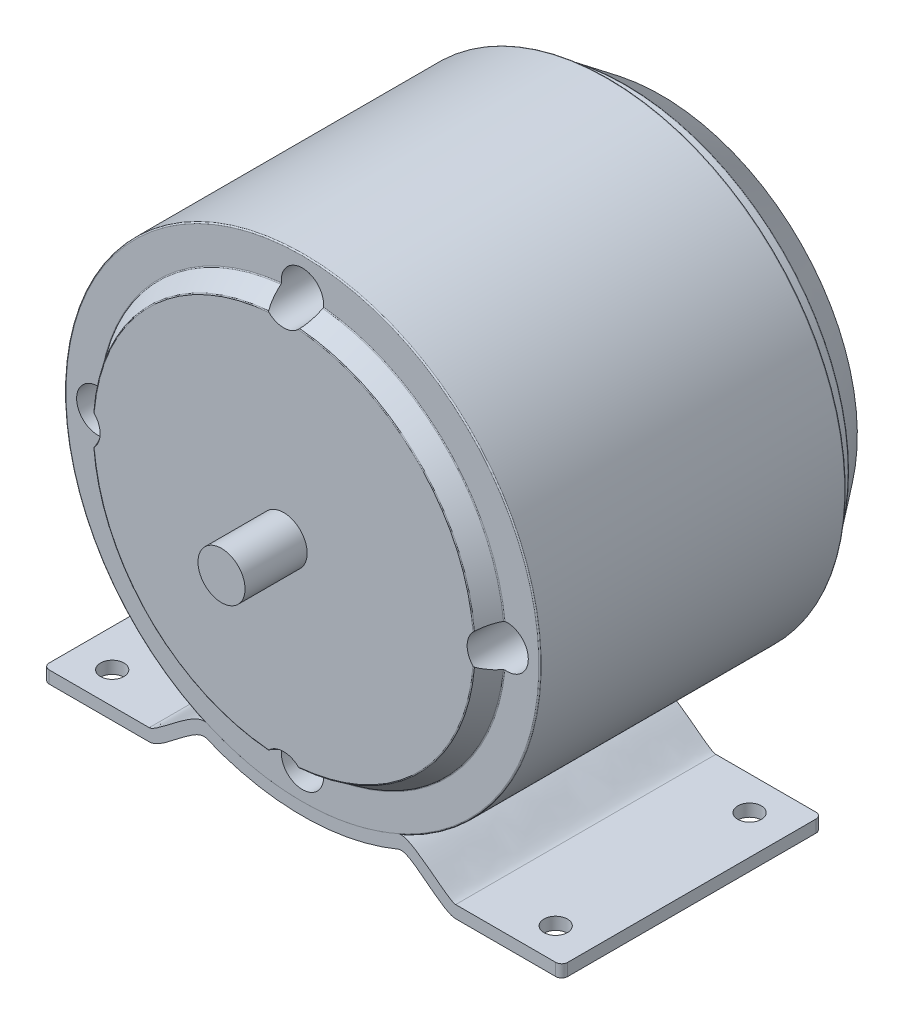
SolidWorks part; units mm, degrees
ref_plane "Front Plane" through (0, 0, 0) normal (0, 0, 1) x (1, 0, 0)
ref_plane "Top Plane" through (0, 0, 0) normal (0, 1, 0) x (1, 0, 0)
ref_plane "Right Plane" through (0, 0, 0) normal (1, 0, 0) x (0, 0, -1)
sketch "Sketch3" plane through (0, 0, 0) normal (1, 0, 0) x (0, 0, -1)
  line L0 (-45, 0) -> (45, 0) construction
  line L1 (-45, 0) -> (-45, 40.3636)
  line L2 (-44.8863, 40.5753) -> (-41.1137, 43.0747)
  line L3 (-41, 43.2864) -> (-41, 50.246)
  line L4 (-40.746, 50.5) -> (23.746, 50.5)
  line L5 (24, 50.246) -> (24, 47.754)
  line L6 (24.254, 47.5) -> (27.4649, 47.5)
  line L7 (27.6179, 47.4487) -> (35.199, 41.7262)
  line L8 (35.3, 41.5235) -> (35.3, 16.504)
  line L9 (35.554, 16.25) -> (43.73, 16.25)
  line L10 (45, 14.98) -> (45, 0)
  line L11 (-45, 0) -> (45, 0)
  arc A0 (-45, 40.3636) -> (-44.8863, 40.5753) centre (-44.746, 40.3636) cw
  arc A1 (-41.1137, 43.0747) -> (-41, 43.2864) centre (-41.254, 43.2864) ccw
  arc A2 (35.3, 16.504) -> (35.554, 16.25) centre (35.554, 16.504) ccw
  arc A3 (35.199, 41.7262) -> (35.3, 41.5235) centre (35.046, 41.5235) cw
  arc A4 (24, 47.754) -> (24.254, 47.5) centre (24.254, 47.754) ccw
  arc A5 (27.4649, 47.5) -> (27.6179, 47.4487) centre (27.4649, 47.246) cw
  arc A6 (23.746, 50.5) -> (24, 50.246) centre (23.746, 50.246) cw
  arc A7 (-41, 50.246) -> (-40.746, 50.5) centre (-40.746, 50.246) cw
  arc A8 (43.73, 16.25) -> (45, 14.98) centre (43.73, 14.98) cw
  point P3 (0, 0)
  point P15 (-45, 40.5)
  point P18 (-41, 43.15)
  point P21 (35.3, 16.25)
  point P24 (35.3, 41.65)
  point P27 (24, 47.5)
  point P30 (27.55, 47.5)
  point P33 (24, 50.5)
  point P36 (-41, 50.5)
  point P39 (45, 16.25)
  dimension "D12" = 0.254
  dimension "D13" = 1.27
  dimension "D1" = 90
  dimension "D2" = 4
  dimension "D3" = 40.5
  dimension "D4" = 50.5
  dimension "D5" = 7.35
  dimension "D6" = 16.25
  dimension "D7" = 9.7
  dimension "D8" = 25.4
  dimension "D9" = 65
  dimension "D10" = 3.55
  dimension "D11" = 3
revolve "Revolve1" add sketch "Sketch3" angle 360 about L0
sketch "Sketch4" plane through (0, 0, 45) normal (0, 0, 1) x (1, 0, 0)
  circle A0 centre (0, 43.5) radius 4.5
  circle A1 centre (43.5, 0) radius 4.5
  circle A2 centre (0, -43.5) radius 4.5
  circle A3 centre (-43.5, 0) radius 4.5
  dimension "D1" = 9
  dimension "D2" = 43.5
  dimension "D3" = 4
extrude "Cut-Extrude1" cut sketch "Sketch4" against normal blind 12.7
sketch "Sketch6" plane through (0, 0, 45) normal (0, 0, 1) x (1, 0, 0)
  circle A0 centre (0, 0) radius 5
  dimension "D1" = 10
extrude "Boss-Extrude3" add sketch "Sketch6" along normal blind 13.2
sketch "Sketch8" plane through (0, 0, 41) normal (0, 0, 1) x (1, 0, 0)
  line L0 (-71.4793, -55.5) -> (69.5208, -55.5) construction
  line L1 (-55.1, -55.5) -> (-32.56, -55.5)
  line L2 (-55.1, -52.88) -> (-32.56, -52.88)
  line L3 (-21.6354, -48.2657) -> (-19.1246, -49.294) construction
  line L4 (-22.2181, -45.1745) -> (-18.5419, -46.6801) construction
  line L5 (-32.5505, -55.5) -> (-29.8576, -55.5) construction
  line L6 (-32.6671, -52.88) -> (-29.7512, -52.88) construction
  line L7 (-55.1, -52.88) -> (-55.1, -55.5)
  line L8 (0, -1000) -> (0, 49000) construction
  line L9 (55.1, -52.88) -> (55.1, -55.5)
  line L10 (55.1, -52.88) -> (32.56, -52.88)
  line L11 (55.1, -55.5) -> (32.56, -55.5)
  arc A0 (-20.38, -45.9273) -> (20.38, -45.9273) centre (0, 0) ccw
  circle A1 centre (0, 0) radius 50.246 construction
  arc A2 (-20.38, -48.7798) -> (20.38, -48.7798) centre (0, 0) ccw
  spline S0 degree 3 poles (-20.38, -48.7798) (-22.9847, -47.7131) (-29.4276, -55.5) (-32.56, -55.5) knots 0 0 0 0 1 1 1 1
  spline S1 degree 3 poles (-20.38, -45.9273) (-23.0001, -44.8543) (-30.7376, -52.88) (-32.56, -52.88) knots 0 0 0 0 1 1 1 1
  spline S2 degree 3 poles (20.38, -48.7798) (22.9847, -47.7131) (29.4276, -55.5) (32.56, -55.5) knots 0 0 0 0 1 1 1 1
  spline S3 degree 3 poles (20.38, -45.9273) (23.0001, -44.8543) (30.7376, -52.88) (32.56, -52.88) knots 0 0 0 0 1 1 1 1
  point P6 (0, -50.246)
  dimension "D4" = 2.62
  dimension "D2" = 55.5
  dimension "D1" = 40.76
  dimension "D3" = 2.62
  dimension "D5" = 12.18
  dimension "D6" = 110.2
extrude "Boss-Extrude6" add sketch "Sketch8" against normal blind 55.3 separate body
fillet "Fillet1" radius 1.27 4 edges at (-55.1, -54.19, -14.3) (-55.1, -54.19, 41) (55.1, -54.19, -14.3) (55.1, -54.19, 41)
sketch "Sketch9" plane through (0, -55.5, 0) normal (0, -1, 0) x (1, 0, 0)
  line L0 (55.1, -13.03) -> (55.1, 39.73) construction
  line L2 (32.56, 41) -> (53.83, 41) construction
  line L3 (32.56, -14.3) -> (53.83, -14.3) construction
  circle A0 centre (47.1, 34.28) radius 2.5
  circle A1 centre (46.87, -7.16) radius 2.5
  dimension "D1" = 8.23
  dimension "D2" = 5
  dimension "D3" = 8
  dimension "D4" = 6.72
  dimension "D5" = 7.14
extrude "Cut-Extrude2" cut sketch "Sketch9" against normal up to next (2.62 mm away)
sketch "Sketch10" plane through (0, -55.5, 0) normal (0, -1, 0) x (1, 0, 0)
  line L0 (-53.83, 41) -> (-32.56, 41) construction
  line L1 (-55.1, -13.03) -> (-55.1, 39.73) construction
  line L2 (-53.83, -14.3) -> (-32.56, -14.3) construction
  circle A0 centre (-47.15, 34.28) radius 2.5
  circle A1 centre (-46.9, -7.36) radius 2.5
  dimension "D1" = 5
  dimension "D2" = 6.72
  dimension "D3" = 7.95
  dimension "D4" = 8.2
  dimension "D5" = 6.94
extrude "Cut-Extrude3" cut sketch "Sketch10" against normal up to next (2.62 mm away)
